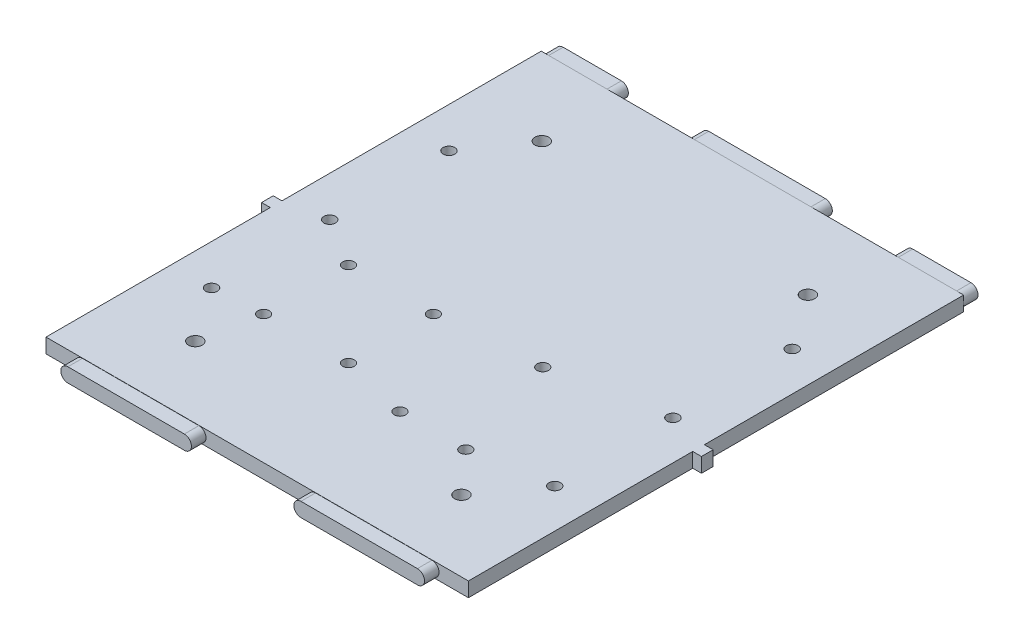
SolidWorks part; units mm, degrees
ref_plane "Front Plane" through (0, 0, 0) normal (0, 0, 1) x (1, 0, 0)
ref_plane "Top Plane" through (0, 0, 0) normal (0, 1, 0) x (1, 0, 0)
ref_plane "Right Plane" through (0, 0, 0) normal (1, 0, 0) x (0, 0, -1)
sketch "Sketch4" plane through (0, 0, 0) normal (0, 1, 0) x (1, 0, 0)
  line L1 (0, 0) -> (184.15, 0)
  line L2 (0, 0) -> (0, 215.9)
  line L3 (0, 215.9) -> (184.15, 215.9)
  line L4 (184.15, 0) -> (184.15, 215.9)
  dimension "D1" = 215.9
  dimension "D2" = 184.15
extrude "Boss-Extrude2" add sketch "Sketch4" along normal blind 6.35
sketch "Sketch5" plane through (0, 0, 0) normal (0, 0, 1) x (1, 0, 0)
  line L0 (92.075, 0) -> (92.075, 6.35) construction
  line L1 (0, 0) -> (184.15, 0) construction
  line L3 (15.875, 3.175) -> (168.275, 3.175) construction
  line L4 (15.875, 3.175) -> (66.675, 3.175) construction
  line L6 (15.875, 6.35) -> (66.675, 6.35)
  line L7 (15.875, 0) -> (66.675, 0)
  arc A0 (15.875, 6.35) -> (15.875, 0) centre (15.875, 3.175) ccw
  arc A1 (66.675, 0) -> (66.675, 6.35) centre (66.675, 3.175) ccw
  point P6 (92.075, 3.175)
  point P7 (92.075, 3.175)
  point P8 (92.075, 6.35)
  point P9 (92.075, 6.35)
  point P13 (41.275, 3.175)
  dimension "D1" = 152.4
extrude "Boss-Extrude3" add sketch "Sketch5" along normal blind 6.35
ref_plane "Plane1" through (92.075, 0, 0) normal (1, 0, 0) x (0, 0, -1)
mirror "Mirror1" about plane through (92.075, 0, 0) normal (1, 0, 0) of "Boss-Extrude3"
ref_plane "Plane2" through (0, 0, -107.95) normal (0, 0, 1) x (1, 0, 0)
sketch "Sketch6" plane through (0, 0, -215.9) normal (0, 0, -1) x (-1, 0, 0)
  line L0 (-184.15, 3.175) -> (0, 3.175) construction
  line L1 (-184.15, 6.35) -> (-184.15, 0) construction
  line L2 (0, 6.35) -> (0, 0) construction
  line L3 (-92.075, 6.35) -> (-92.075, 0) construction
  line L4 (-184.15, 6.35) -> (0, 6.35) construction
  line L5 (-184.15, 0) -> (0, 0) construction
  line L6 (-117.475, 3.175) -> (-66.675, 3.175) construction
  line L7 (-28.575, 3.175) -> (-3.175, 3.175) construction
  line L8 (-117.475, 6.35) -> (-66.675, 6.35)
  line L9 (-117.475, 0) -> (-66.675, 0)
  line L10 (-28.575, 6.35) -> (-3.175, 6.35)
  line L11 (-28.575, 0) -> (-3.175, 0)
  line L12 (-155.575, 3.175) -> (-180.975, 3.175) construction
  line L13 (-155.575, 6.35) -> (-180.975, 6.35)
  line L14 (-155.575, 0) -> (-180.975, 0)
  arc A0 (-117.475, 6.35) -> (-117.475, 0) centre (-117.475, 3.175) ccw
  arc A1 (-66.675, 0) -> (-66.675, 6.35) centre (-66.675, 3.175) ccw
  arc A2 (-28.575, 6.35) -> (-28.575, 0) centre (-28.575, 3.175) ccw
  arc A3 (-3.175, 0) -> (-3.175, 6.35) centre (-3.175, 3.175) ccw
  arc A4 (-155.575, 6.35) -> (-155.575, 0) centre (-155.575, 3.175) cw
  arc A5 (-180.975, 0) -> (-180.975, 6.35) centre (-180.975, 3.175) cw
  point P16 (-92.075, 3.175)
  point P21 (-15.875, 3.175)
  point P28 (-168.275, 3.175)
  dimension "D1" = 50.8
  dimension "D2" = 25.4
  dimension "D3" = 76.2
extrude "Boss-Extrude4" add sketch "Sketch6" along normal blind 6.35
mirror "Mirror2" [suppressed] about plane through (0, 0, -107.95) normal (0, 0, 1)
sketch "Sketch7" plane through (184.15, 0, 0) normal (1, 0, 0) x (0, 0, -1)
  line L0 (0, 0) -> (215.9, 0) construction
  line L1 (102.87, 0) -> (97.79, 0)
  line L2 (102.87, 0) -> (102.87, 6.35)
  line L3 (102.87, 6.35) -> (97.79, 6.35)
  line L4 (97.79, 0) -> (97.79, 6.35)
  line L5 (0, 6.35) -> (215.9, 6.35) construction
  line L7 (-6.35, 6.35) -> (-6.35, 0) construction
  dimension "D1" = 109.22
  dimension "D2" = 5.08
extrude "Boss-Extrude5" add sketch "Sketch7" along normal blind 3.81
ref_plane "Plane3" through (92.075, 0, 0) normal (-1, 0, 0) x (0, 0, 1)
mirror "Mirror3" about plane through (92.075, 0, 0) normal (-1, 0, 0) of "Boss-Extrude5"
sketch "Sketch8" [suppressed] plane through (0, 6.35, 0) normal (0, 1, 0) x (1, 0, 0)
  line L0 (187.96, 102.87) -> (184.15, 102.87) construction
  line L1 (202.2548, 102.87) -> (-20.7921, 102.87)
  line L2 (202.2548, 102.87) -> (202.2548, 222.25)
  line L3 (202.2548, 222.25) -> (-20.7921, 222.25)
  line L4 (-20.7921, 102.87) -> (-20.7921, 222.25)
  line L5 (66.675, 222.25) -> (117.475, 222.25) construction
extrude "Cut-Extrude1" [suppressed] cut sketch "Sketch8" against normal through all
sketch "Sketch9" [suppressed] plane through (0, 0, -102.87) normal (0, 0, -1) x (-1, 0, 0)
  line L0 (-187.96, 3.175) -> (3.81, 3.175) construction
  line L1 (-187.96, 0) -> (-187.96, 6.35) construction
  line L2 (3.81, 0) -> (3.81, 6.35) construction
  line L3 (-92.075, 6.35) -> (-92.075, 0) construction
  line L4 (-187.96, 6.35) -> (3.81, 6.35) construction
  line L5 (-187.96, 0) -> (3.81, 0) construction
  line L7 (-117.475, 1.905) -> (-66.675, 1.905)
  line L8 (-117.475, 1.905) -> (-117.475, 4.445)
  line L9 (-117.475, 4.445) -> (-66.675, 4.445)
  line L10 (-66.675, 1.905) -> (-66.675, 4.445)
  dimension "D1" = 50.8
  dimension "D2" = 2.54
extrude "Cut-Extrude2" [suppressed] cut sketch "Sketch9" against normal blind 12.7
sketch "Sketch10" [suppressed] plane through (0, 6.35, 0) normal (0, 1, 0) x (1, 0, 0)
  line L0 (187.96, 102.87) -> (184.15, 102.87) construction
  line L1 (-36.6174, 102.87) -> (214.1984, 102.87)
  line L2 (-36.6174, 102.87) -> (-36.6174, -17.7605)
  line L3 (-36.6174, -17.7605) -> (214.1984, -17.7605)
  line L4 (214.1984, 102.87) -> (214.1984, -17.7605)
extrude "Cut-Extrude3" [suppressed] cut sketch "Sketch10" against normal through all
sketch "Sketch11" [suppressed] plane through (0, 0, -102.87) normal (0, 0, 1) x (1, 0, 0)
  line L0 (0, 3.175) -> (184.15, 3.175) construction
  line L1 (0, 0) -> (0, 6.35) construction
  line L2 (184.15, 0) -> (184.15, 6.35) construction
  line L3 (92.075, 6.35) -> (92.075, 0) construction
  line L4 (184.15, 6.35) -> (0, 6.35) construction
  line L5 (184.15, 0) -> (0, 0) construction
  line L7 (66.675, 4.445) -> (117.475, 4.445)
  line L8 (66.675, 4.445) -> (66.675, 1.905)
  line L9 (66.675, 1.905) -> (117.475, 1.905)
  line L10 (117.475, 4.445) -> (117.475, 1.905)
  dimension "D1" = 50.8
  dimension "D2" = 2.54
extrude "Boss-Extrude6" [suppressed] add sketch "Sketch11" along normal blind 12.7
sketch "Sketch12" plane through (0, 0, 0) normal (0, -1, 0) x (1, 0, 0)
  circle A0 centre (17.5286, -54.65) radius 2.54
  circle A1 centre (167.15, -54.65) radius 2.54
  circle A2 centre (167.15, -106.15) radius 2.54
  circle A3 centre (17.5286, -106.15) radius 2.54
  circle A4 centre (17.5286, -158.15) radius 2.54
  circle A5 centre (167.15, -158.15) radius 2.54
  circle A6 centre (17.5286, -54.65) radius 2.54 construction
  circle A7 centre (167.15, -54.65) radius 2.54 construction
  circle A8 centre (167.15, -106.15) radius 2.54 construction
  circle A9 centre (17.5286, -106.15) radius 2.54 construction
  circle A10 centre (17.5286, -158.15) radius 2.54 construction
  circle A11 centre (167.15, -158.15) radius 2.54 construction
extrude "Cut-Extrude4" cut sketch "Sketch12" against normal through all
sketch "Sketch13" [suppressed] plane through (0, 6.35, 0) normal (0, 1, 0) x (1, 0, 0)
  line L0 (187.96, 102.87) -> (184.15, 102.87) construction
  line L1 (-19.5978, 102.87) -> (203.8672, 102.87)
  line L2 (-19.5978, 102.87) -> (-19.5978, 233.4435)
  line L3 (-19.5978, 233.4435) -> (203.8672, 233.4435)
  line L4 (203.8672, 102.87) -> (203.8672, 233.4435)
extrude "Cut-Extrude5" [suppressed] cut sketch "Sketch13" against normal through all
sketch "Sketch14" [suppressed] plane through (0, 0, -102.87) normal (0, 0, -1) x (-1, 0, 0)
  line L0 (-187.96, 3.175) -> (3.81, 3.175) construction
  line L1 (-187.96, 0) -> (-187.96, 6.35) construction
  line L2 (3.81, 0) -> (3.81, 6.35) construction
  line L3 (-92.075, 6.35) -> (-92.075, 0) construction
  line L4 (-187.96, 6.35) -> (3.81, 6.35) construction
  line L5 (-187.96, 0) -> (3.81, 0) construction
  line L7 (-104.775, 1.27) -> (-79.375, 1.27)
  line L8 (-104.775, 1.27) -> (-104.775, 5.08)
  line L9 (-104.775, 5.08) -> (-79.375, 5.08)
  line L10 (-79.375, 1.27) -> (-79.375, 5.08)
  dimension "D1" = 25.4
  dimension "D2" = 3.81
extrude "Cut-Extrude6" [suppressed] cut sketch "Sketch14" against normal blind 12.7
sketch "Sketch15" [suppressed] plane through (0, 6.35, 0) normal (0, 1, 0) x (1, 0, 0)
  line L0 (187.96, 102.87) -> (184.15, 102.87) construction
  line L1 (-20.4935, 102.87) -> (198.9703, 102.87)
  line L2 (-20.4935, 102.87) -> (-20.4935, -20.4478)
  line L3 (-20.4935, -20.4478) -> (198.9703, -20.4478)
  line L4 (198.9703, 102.87) -> (198.9703, -20.4478)
extrude "Cut-Extrude7" [suppressed] cut sketch "Sketch15" against normal through all
sketch "Sketch16" [suppressed] plane through (0, 0, -102.87) normal (0, 0, 1) x (1, 0, 0)
  line L0 (0, 3.175) -> (184.15, 3.175) construction
  line L1 (92.075, 6.35) -> (92.075, 0) construction
  line L2 (184.15, 6.35) -> (0, 6.35) construction
  line L3 (184.15, 0) -> (0, 0) construction
  line L5 (79.502, 1.397) -> (104.648, 1.397)
  line L6 (79.502, 1.397) -> (79.502, 4.953)
  line L7 (79.502, 4.953) -> (104.648, 4.953)
  line L8 (104.648, 1.397) -> (104.648, 4.953)
  dimension "D1" = 25.146
  dimension "D2" = 3.556
extrude "Boss-Extrude8" [suppressed] add sketch "Sketch16" along normal blind 12.446
sketch "Sketch18" plane through (0, 6.35, 0) normal (0, 1, 0) x (1, 0, 0)
  circle A0 centre (105.2902, 49.0151) radius 2.5
  circle A1 centre (133.9902, 49.0151) radius 2.5
  circle A2 centre (119.6402, 96.9151) radius 2.5
  dimension "D1" = 5
extrude "Cut-Extrude8" cut sketch "Sketch18" against normal blind 10
sketch "Sketch19" plane through (0, 6.35, 0) normal (0, 1, 0) x (1, 0, 0)
  circle A0 centre (75.7549, 56.1242) radius 2.5
  circle A1 centre (38.7549, 56.1242) radius 2.5
  circle A2 centre (75.7549, 93.1242) radius 2.5
  circle A3 centre (38.7549, 93.1242) radius 2.5
  dimension "D1" = 5
extrude "Cut-Extrude9" cut sketch "Sketch19" against normal blind 10
sketch "Sketch20" plane through (0, 0, 0) normal (0, -1, 0) x (1, 0, 0)
  circle A0 centre (150.1, -182.0483) radius 3
  circle A1 centre (34.1, -182.0483) radius 3
  circle A2 centre (150.1, -31) radius 3
  circle A3 centre (34.1, -31) radius 3
  dimension "6" = 6
extrude "Cut-Extrude10" cut sketch "Sketch20" against normal through all
sketch "Sketch21" plane through (0, 0, -222.25) normal (0, 0, -1) x (-1, 0, 0)
  line L2 (-155.575, 6.35) -> (-180.975, 6.35) construction
  line L3 (-180.975, 0) -> (-155.575, 0) construction
  line L4 (-155.575, 6.25) -> (-180.975, 6.25)
  line L5 (-180.975, 0.1) -> (-155.575, 0.1)
  line L6 (-155.575, 6.25) -> (-180.975, 6.25)
  line L7 (-180.975, 0.1) -> (-155.575, 0.1)
  line L8 (-155.575, 6.35) -> (-180.975, 6.35)
  line L9 (-180.975, 0) -> (-155.575, 0)
  arc A2 (-180.975, 6.35) -> (-180.975, 0) centre (-180.975, 3.175) ccw construction
  arc A3 (-155.575, 0) -> (-155.575, 6.35) centre (-155.575, 3.175) ccw construction
  arc A4 (-155.575, 0.1) -> (-155.575, 6.25) centre (-155.575, 3.175) ccw
  arc A5 (-180.975, 6.25) -> (-180.975, 0.1) centre (-180.975, 3.175) ccw
  arc A6 (-155.575, 0.1) -> (-155.575, 6.25) centre (-155.575, 3.175) ccw
  arc A7 (-180.975, 6.25) -> (-180.975, 0.1) centre (-180.975, 3.175) ccw
  arc A8 (-180.975, 6.35) -> (-180.975, 0) centre (-180.975, 3.175) ccw
  arc A9 (-155.575, 0) -> (-155.575, 6.35) centre (-155.575, 3.175) ccw
  dimension "D1" = 0.1
extrude "Cut-Extrude11" cut sketch "Sketch21" against normal up to surface (6.35 mm away) up to face at (136.525, 3.175, -215.9)
sketch "Sketch22" plane through (0, 0, -222.25) normal (0, 0, -1) x (-1, 0, 0)
  line L0 (-66.675, 6.35) -> (-117.475, 6.35) construction
  line L1 (-117.475, 0) -> (-66.675, 0) construction
  line L2 (-66.675, 6.35) -> (-117.475, 6.35)
  line L3 (-117.475, 0) -> (-66.675, 0)
  line L4 (-66.675, 6.25) -> (-117.475, 6.25)
  line L5 (-117.475, 0.1) -> (-66.675, 0.1)
  arc A0 (-66.675, 0) -> (-66.675, 6.35) centre (-66.675, 3.175) ccw construction
  arc A1 (-117.475, 6.35) -> (-117.475, 0) centre (-117.475, 3.175) ccw construction
  arc A2 (-66.675, 0) -> (-66.675, 6.35) centre (-66.675, 3.175) ccw
  arc A3 (-117.475, 6.35) -> (-117.475, 0) centre (-117.475, 3.175) ccw
  arc A4 (-117.475, 6.25) -> (-117.475, 0.1) centre (-117.475, 3.175) ccw
  arc A5 (-66.675, 0.1) -> (-66.675, 6.25) centre (-66.675, 3.175) ccw
  dimension "D1" = 0.1
extrude "Cut-Extrude12" cut sketch "Sketch22" against normal up to surface (6.35 mm away) up to face at (47.625, 3.175, -215.9)
sketch "Sketch23" plane through (0, 0, -222.25) normal (0, 0, -1) x (-1, 0, 0)
  line L0 (-28.575, 0.1) -> (-3.175, 0.1)
  line L1 (-3.175, 6.25) -> (-28.575, 6.25)
  line L2 (-28.575, 0) -> (-3.175, 0)
  line L3 (-3.175, 6.35) -> (-28.575, 6.35)
  line L4 (-28.575, 0) -> (-3.175, 0)
  line L5 (-3.175, 6.35) -> (-28.575, 6.35)
  arc A0 (-3.175, 0.1) -> (-3.175, 6.25) centre (-3.175, 3.175) ccw
  arc A1 (-28.575, 6.25) -> (-28.575, 0.1) centre (-28.575, 3.175) ccw
  arc A2 (-28.575, 6.35) -> (-28.575, 0) centre (-28.575, 3.175) ccw
  arc A3 (-3.175, 0) -> (-3.175, 6.35) centre (-3.175, 3.175) ccw
  arc A4 (-28.575, 6.35) -> (-28.575, 0) centre (-28.575, 3.175) ccw
  arc A5 (-3.175, 0) -> (-3.175, 6.35) centre (-3.175, 3.175) ccw
  dimension "D1" = 0
  dimension "D2" = 0.1
extrude "Cut-Extrude13" cut sketch "Sketch23" against normal up to surface (6.35 mm away) up to face at (0.8391, 0.8391, -215.9)
sketch "Sketch24" plane through (0, 0, 6.35) normal (0, 0, 1) x (1, 0, 0)
  line L0 (15.875, 0.1) -> (66.675, 0.1)
  line L1 (66.675, 6.25) -> (15.875, 6.25)
  line L2 (15.875, 0) -> (66.675, 0)
  line L3 (66.675, 6.35) -> (15.875, 6.35)
  line L4 (15.875, 0) -> (66.675, 0)
  line L5 (66.675, 6.35) -> (15.875, 6.35)
  arc A0 (66.675, 0.1) -> (66.675, 6.25) centre (66.675, 3.175) ccw
  arc A1 (15.875, 6.25) -> (15.875, 0.1) centre (15.875, 3.175) ccw
  arc A2 (15.875, 6.35) -> (15.875, 0) centre (15.875, 3.175) ccw
  arc A3 (66.675, 0) -> (66.675, 6.35) centre (66.675, 3.175) ccw
  arc A4 (15.875, 6.35) -> (15.875, 0) centre (15.875, 3.175) ccw
  arc A5 (66.675, 0) -> (66.675, 6.35) centre (66.675, 3.175) ccw
  dimension "D1" = 0
  dimension "D2" = 0.1
extrude "Cut-Extrude14" cut sketch "Sketch24" against normal up to surface (6.35 mm away) up to face at (7.1437, 3.175, 0)
sketch "Sketch25" plane through (0, 0, 6.35) normal (0, 0, 1) x (1, 0, 0)
  line L0 (168.275, 6.25) -> (117.475, 6.25)
  line L1 (117.475, 0.1) -> (168.275, 0.1)
  line L2 (168.275, 6.35) -> (117.475, 6.35)
  line L3 (117.475, 0) -> (168.275, 0)
  line L4 (168.275, 6.35) -> (117.475, 6.35)
  line L5 (117.475, 0) -> (168.275, 0)
  arc A0 (117.475, 6.25) -> (117.475, 0.1) centre (117.475, 3.175) ccw
  arc A1 (168.275, 0.1) -> (168.275, 6.25) centre (168.275, 3.175) ccw
  arc A2 (168.275, 0) -> (168.275, 6.35) centre (168.275, 3.175) ccw
  arc A3 (117.475, 6.35) -> (117.475, 0) centre (117.475, 3.175) ccw
  arc A4 (168.275, 0) -> (168.275, 6.35) centre (168.275, 3.175) ccw
  arc A5 (117.475, 6.35) -> (117.475, 0) centre (117.475, 3.175) ccw
  dimension "D1" = 0
  dimension "D2" = 0.1
extrude "Cut-Extrude15" cut sketch "Sketch25" against normal up to surface (6.35 mm away) up to face at (57.9438, 3.175, 0)
